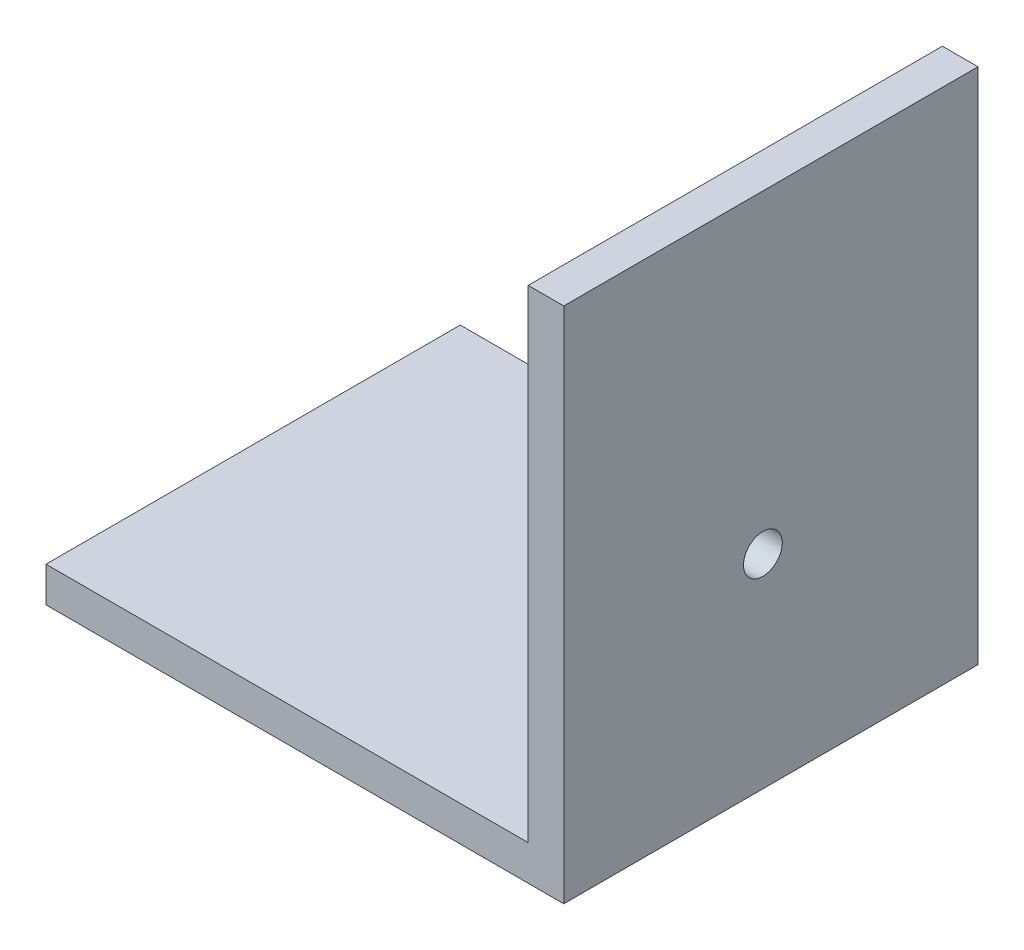
SolidWorks part; units mm, degrees
ref_plane "Front Plane" through (0, 0, 0) normal (0, 0, 1) x (1, 0, 0)
ref_plane "Top Plane" through (0, 0, 0) normal (0, 1, 0) x (1, 0, 0)
ref_plane "Right Plane" through (0, 0, 0) normal (1, 0, 0) x (0, 0, -1)
sketch "Sketch1" plane through (0, 0, 0) normal (0, 0, 1) x (1, 0, 0)
  line L1 (-63.5, 4.318) -> (63.5, 4.318)
  line L2 (-63.5, 4.318) -> (-63.5, -4.318)
  line L3 (-63.5, -4.318) -> (63.5, -4.318)
  line L4 (63.5, 4.318) -> (63.5, -4.318)
  point P4 (0, 4.318)
  point P5 (63.5, 0)
  dimension "D1" = 8.636
  dimension "D2" = 127
extrude "Boss-Extrude1" add sketch "Sketch1" along normal blind 101.6
sketch "Sketch3" plane through (0, 0, 101.6) normal (0, 0, 1) x (1, 0, 0)
  line L1 (63.5, -4.318) -> (54.7624, -4.318)
  line L2 (63.5, -4.318) -> (63.5, 122.682)
  line L3 (63.5, 122.682) -> (54.7624, 122.682)
  line L4 (-63.5, 4.318) -> (-63.5, -4.318)
  line L5 (-63.5, -4.318) -> (63.5, -4.318)
  line L6 (63.5, -4.318) -> (63.5, 4.318)
  line L7 (63.5, 4.318) -> (-63.5, 4.318)
  line L8 (-63.5, 4.318) -> (-63.5, -4.318)
  line L9 (-63.5, -4.318) -> (63.5, -4.318)
  line L10 (63.5, -4.318) -> (63.5, 4.318)
  line L11 (63.5, 4.318) -> (-63.5, 4.318)
  line L12 (54.7624, -4.318) -> (54.7624, 122.682)
  line M10 (63.5, 4.318) -> (-63.5, 4.318)
  dimension "D2" = 8.7376
  dimension "D3" = 127
  dimension "D1" = 0
extrude "Boss-Extrude2" add sketch "Sketch3" against normal through all contours L12 L2 L3 M10
hole_wizard "1/2 (0.5000) Dowel Hole2" positions "3DSketch4" profile "Sketch7" hole size "1/2" standard "ANSI Inch" end condition through all
sketch3d "3DSketch4"
  line L0 (54.7624, 4.318, 0) -> (54.7624, 4.318, 101.6) construction
  line L1 (54.7624, 4.318, 0) -> (-63.5, 4.318, 0) construction
  point P0 (16.6624, 4.318, 50.8)
  dimension "D1" = 38.1
  dimension "D2" = 50.8
sketch "Sketch7" plane through (16.6624, 4.318, 50.8) normal (1, 0, 0) x (0, 0, 1)
  line L0 (0, 0) -> (0, 8.636)
  line L1 (0, 8.636) -> (6.35, 8.636)
  line L2 (6.35, 8.636) -> (6.35, 0)
  line L5 (6.35, 0) -> (0, 0)
  line L11 (0, -6.35) -> (0, 107.95) construction
  dimension "Thru Hole Dia." = 12.7
  dimension "Thru Hole Depth" = 8.636
hole_wizard "3/8 (0.3750) Dowel Hole3" positions "3DSketch5" profile "Sketch8" hole size "3/8" standard "ANSI Inch" end condition through all
sketch3d "3DSketch5"
  line L0 (54.7624, 4.318, 0) -> (54.7624, 4.318, 101.6) construction
  point P0 (54.7624, 45.593, 52.7654)
  dimension "D1" = 41.275
sketch "Sketch8" plane through (54.7624, 45.593, 52.7654) normal (0, 1, 0) x (0, 0, 1)
  line L0 (0, 0) -> (0, 8.7376)
  line L1 (0, 8.7376) -> (4.7625, 8.7376)
  line L2 (4.7625, 8.7376) -> (4.7625, 0)
  line L5 (4.7625, 0) -> (0, 0)
  line L11 (0, -6.35) -> (0, 107.95) construction
  dimension "Thru Hole Dia." = 9.525
  dimension "Thru Hole Depth" = 8.7376
